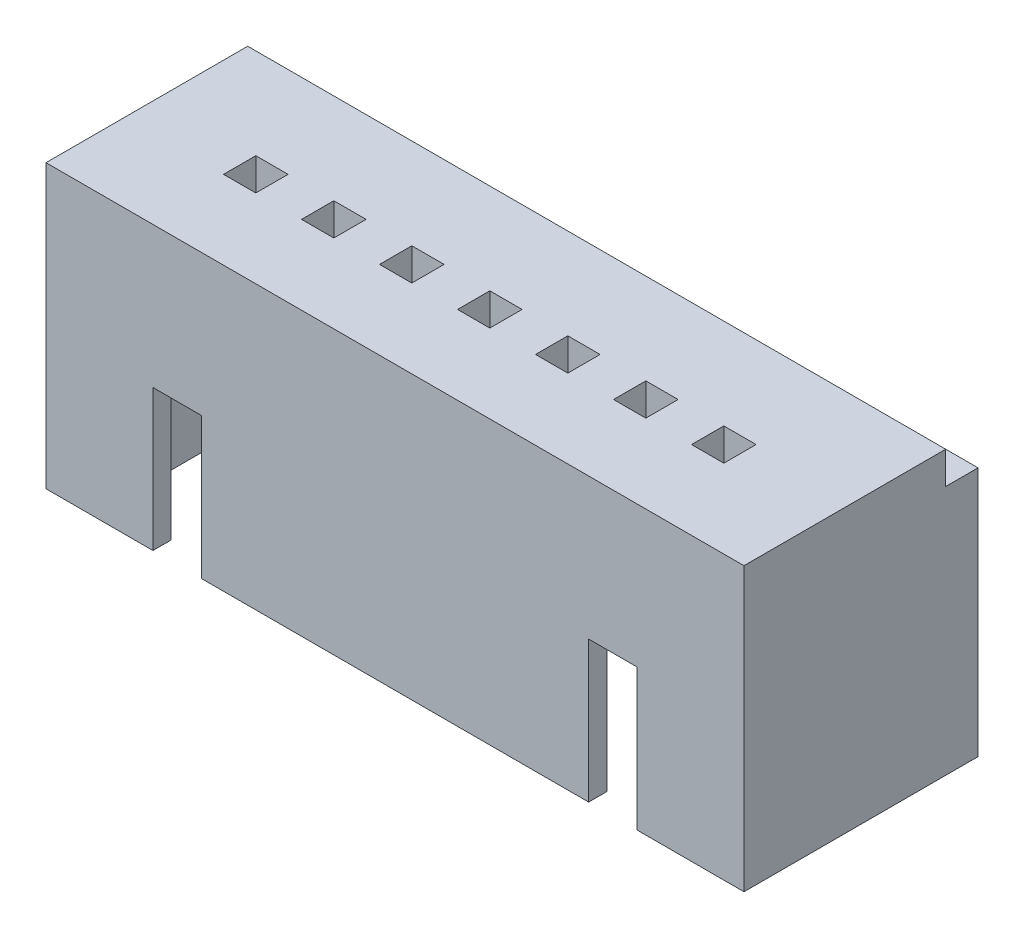
SolidWorks part; units mm, degrees
ref_plane "Front Plane" through (0, 0, 0) normal (0, 0, 1) x (1, 0, 0)
ref_plane "Top Plane" through (0, 0, 0) normal (0, 1, 0) x (1, 0, 0)
ref_plane "Right Plane" through (0, 0, 0) normal (1, 0, 0) x (0, 0, -1)
sketch "Sketch1" plane through (0, 0, 0) normal (0, 1, 0) x (1, 0, 0)
  line L1 (-8.65, -2.9) -> (8.65, -2.9)
  line L2 (-8.65, -2.9) -> (-8.65, 2.9)
  line L3 (-8.65, 2.9) -> (8.65, 2.9)
  line L4 (8.65, -2.9) -> (8.65, 2.9)
  line L5 (-8.65, -2.9) -> (8.65, 2.9) construction
  line L6 (-8.65, 2.9) -> (8.65, -2.9) construction
  point P0 (0, 0)
  dimension "D1" = 17.3
  dimension "D2" = 5.8
extrude "Boss-Extrude1" add sketch "Sketch1" along normal blind 7
sketch "Sketch3" plane through (0, 0, 0) normal (0, -1, 0) x (1, 0, 0)
  line L1 (-7.5, -2.45) -> (7.5, -2.45)
  line L2 (-7.5, -2.45) -> (-7.5, 2.45)
  line L3 (-7.5, 2.45) -> (7.5, 2.45)
  line L4 (7.5, -2.45) -> (7.5, 2.45)
  line L5 (-7.5, -2.45) -> (7.5, 2.45) construction
  line L6 (-7.5, 2.45) -> (7.5, -2.45) construction
  point P0 (0, 0)
  dimension "D1" = 15
  dimension "D2" = 4.9
extrude "Cut-Extrude1" cut sketch "Sketch3" against normal blind 5
sketch "Sketch4" plane through (0, 0, 2.9) normal (0, 0, 1) x (1, 0, 0)
  line L0 (-8.65, 0) -> (8.65, 0) construction
  line L1 (-6, 0) -> (-4.8, 0)
  line L2 (-6, 0) -> (-6, 3.5)
  line L3 (-6, 3.5) -> (-4.8, 3.5)
  line L4 (-4.8, 0) -> (-4.8, 3.5)
  line L6 (4.8, 0) -> (6, 0)
  line L7 (4.8, 0) -> (4.8, 3.5)
  line L8 (4.8, 3.5) -> (6, 3.5)
  line L9 (6, 0) -> (6, 3.5)
  dimension "D1" = 1.2
  dimension "D2" = 1.2
  dimension "D3" = 6
  dimension "D4" = 12
  dimension "D5" = 3.5
extrude "Cut-Extrude2" cut sketch "Sketch4" against normal blind 4
sketch "Sketch5" plane through (0, 7, 0) normal (0, 1, 0) x (1, 0, 0)
  line L0 (8.65, -2.9) -> (8.65, 2.9) construction
  line L1 (8.65, 2.1) -> (-8.65, 2.1)
  line L2 (8.65, 2.1) -> (8.65, 2.9)
  line L3 (8.65, 2.9) -> (-8.65, 2.9)
  line L4 (-8.65, 2.1) -> (-8.65, 2.9)
  dimension "D1" = 0.8
extrude "Cut-Extrude3" cut sketch "Sketch5" against normal blind 0.8 contours L1 L4 L3 L2
sketch "Sketch6" plane through (0, 7, 0) normal (0, 1, 0) x (1, 0, 0)
  line L1 (-2.3333, -0.15) -> (-2.3333, -0.95) construction
  line L2 (6.2, -0.95) -> (5.4, -0.95)
  line L3 (6.2, -0.95) -> (6.2, -0.15)
  line L4 (6.2, -0.15) -> (5.4, -0.15)
  line L5 (5.4, -0.95) -> (5.4, -0.15)
  line L6 (4.2667, -0.95) -> (3.4667, -0.95)
  line L7 (4.2667, -0.95) -> (4.2667, -0.15)
  line L8 (4.2667, -0.15) -> (3.4667, -0.15)
  line L9 (3.4667, -0.95) -> (3.4667, -0.15)
  line L10 (2.3333, -0.95) -> (1.5333, -0.95)
  line L11 (2.3333, -0.95) -> (2.3333, -0.15)
  line L12 (2.3333, -0.15) -> (1.5333, -0.15)
  line L13 (1.5333, -0.95) -> (1.5333, -0.15)
  line L14 (0.4, -0.95) -> (-0.4, -0.95)
  line L15 (0.4, -0.95) -> (0.4, -0.15)
  line L16 (0.4, -0.15) -> (-0.4, -0.15)
  line L17 (-0.4, -0.95) -> (-0.4, -0.15)
  line L18 (-1.5333, -0.95) -> (-2.3333, -0.95)
  line L19 (-1.5333, -0.95) -> (-1.5333, -0.15)
  line L20 (-1.5333, -0.15) -> (-2.3333, -0.15)
  line L21 (-2.3333, -0.95) -> (-2.3333, -0.15)
  line L23 (-3.4667, -0.95) -> (-4.2667, -0.95)
  line L24 (-3.4667, -0.95) -> (-3.4667, -0.15)
  line L25 (-3.4667, -0.15) -> (-4.2667, -0.15)
  line L26 (-4.2667, -0.95) -> (-4.2667, -0.15)
  line L27 (-5.4, -0.95) -> (-6.2, -0.95)
  line L28 (-5.4, -0.95) -> (-5.4, -0.15)
  line L29 (-5.4, -0.15) -> (-6.2, -0.15)
  line L30 (-6.2, -0.95) -> (-6.2, -0.15)
extrude "Cut-Extrude4" cut sketch "Sketch6" against normal blind 10
sketch "Sketch7" plane through (0, 5, 0) normal (0, -1, 0) x (1, 0, 0)
  line L0 (7.5, -2.45) -> (7.5, 2.45) construction
  line L1 (-7.5, -2.45) -> (7.5, -2.45)
  line L2 (-7.5, -2.45) -> (-7.5, -1.45)
  line L3 (-7.5, -1.45) -> (7.5, -1.45)
  line L4 (7.5, -2.45) -> (7.5, -1.45)
  dimension "D1" = 1
extrude "Cut-Extrude5" cut sketch "Sketch7" against normal blind 0.3
